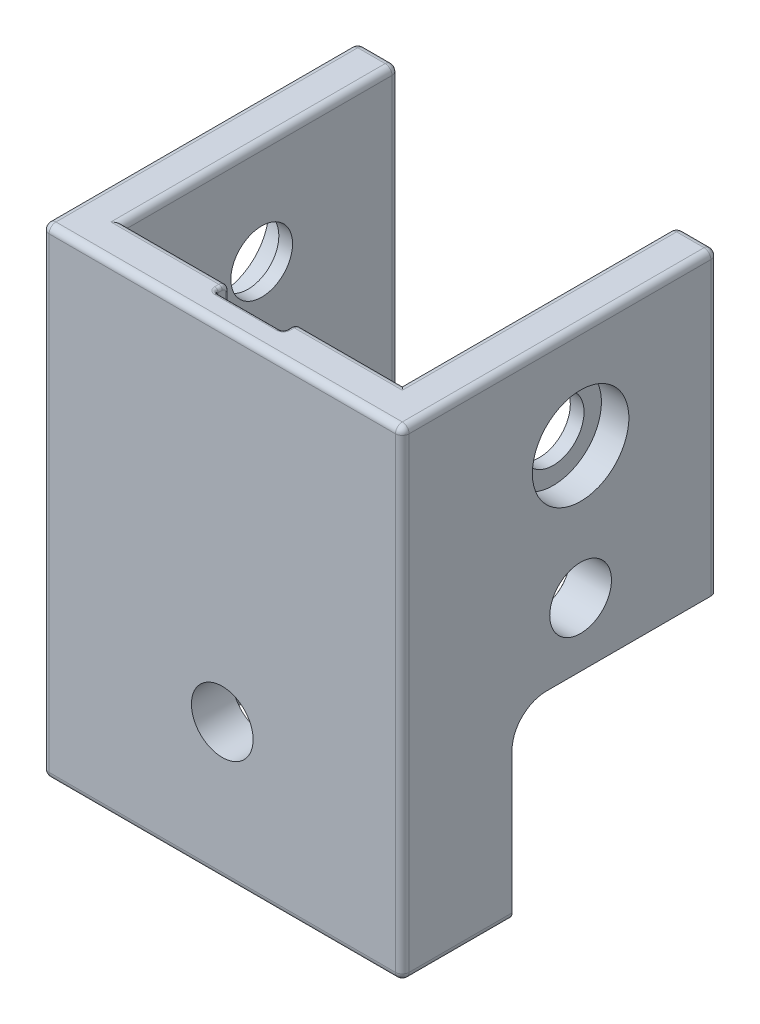
SolidWorks part; units mm, degrees
ref_plane "Front Plane" through (0, 0, 0) normal (0, 0, 1) x (1, 0, 0)
ref_plane "Top Plane" through (0, 0, 0) normal (0, 1, 0) x (1, 0, 0)
ref_plane "Right Plane" through (0, 0, 0) normal (1, 0, 0) x (0, 0, -1)
sketch "Sketch1" plane through (0, 0, 0) normal (0, 1, 0) x (1, 0, 0)
  line L1 (-26.25, -26.25) -> (26.25, -26.25)
  line L2 (-26.25, -26.25) -> (-26.25, 19.75)
  line L4 (26.25, -26.25) -> (26.25, 19.75)
  line L5 (-26.25, -26.25) -> (-20.25, -20.25) construction
  line L6 (20.25, -20.25) -> (26.25, -26.25) construction
  line L11 (-20.25, 19.75) -> (-20.25, -20.25)
  line L12 (-20.25, -20.25) -> (20.25, -20.25)
  line L20 (-20.25, 19.75) -> (-26.25, 19.75)
  line L21 (20.25, 19.75) -> (26.25, 19.75)
  line L22 (20.25, -20.25) -> (20.25, 19.75)
  point P0 (0, 0)
  point P5 (0, 0)
  point P47 (0, 0.8)
  point P49 (0, 0)
  dimension "D1" = 40.5
  dimension "D2" = 6
  dimension "D3" = 6
  dimension "D4" = 46
  dimension "D5" = 6
  dimension "D6" = 46
extrude "Boss-Extrude1" add sketch "Sketch1" along normal blind 70
ref_plane "Plane2" through (20.25, 0, -19.75) normal (1, 0, 0) x (0, 0, -1)
sketch "Sketch8" plane through (26.25, 0, 0) normal (1, 0, 0) x (0, 0, -1)
  line L0 (19.75, 70) -> (19.75, 0) construction
  line L2 (-26.25, 70) -> (19.75, 70) construction
  circle A0 centre (-0.25, 55) radius 4.5
  dimension "D1" = 20
  dimension "D3" = 9
  dimension "D2" = 15
extrude "Cut-Extrude4" cut sketch "Sketch8" against normal through all
sketch "Sketch10" plane through (-26.25, 0, 0) normal (-1, 0, 0) x (0, 0, 1)
  circle A0 centre (0.25, 55) radius 7.035
  dimension "D1" = 14.07
extrude "Cut-Extrude5" cut sketch "Sketch10" against normal blind 4
mirror "Mirror1" about plane through (0, 0, 0) normal (1, 0, 0) of "Cut-Extrude5"
fillet "Fillet13" radius 1 22 edges at (26.25, 0, 3.25) (0, 0, 26.25) (-26.25, 0, 3.25) (-23.25, 0, -19.75) (-26.25, 35, 26.25) (0, 70, 26.25) (-26.25, 70, 3.25) (23.25, 70, -19.75) (-23.25, 70, -19.75) (26.25, 70, 3.25) (26.25, 35, -19.75) (-26.25, 35, -19.75) (26.25, 35, 26.25) (23.25, 0, -19.75) (20.25, 0, 0.25) (-20.25, 0, 0.25) (0, 0, 20.25) (20.25, 70, 0.25) (-20.25, 70, 0.25) (0, 70, 20.25) (-20.25, 35, -19.75) (20.25, 35, -19.75)
sketch "Sketch15" plane through (-26.25, 0, 0) normal (-1, 0, 0) x (0, 0, 1)
  line L0 (-19.75, 1) -> (-19.75, 69) construction
  line L1 (-18.75, 70) -> (25.25, 70) construction
  point P0 (-14.75, 40)
  point P2 (15.25, 40)
  point P4 (15.25, 15)
  point P6 (-14.75, 15)
  dimension "D1" = 5
  dimension "D2" = 35
  dimension "D3" = 25
  dimension "D4" = 30
hole_wizard "M8 Clearance Hole1" positions "Sketch19" profile "Sketch18" hole size "M8" standard "ANSI Metric"
sketch "Sketch19" plane through (-20.25, 0, 0) normal (1, 0, 0) x (0, 0, -1)
  line L0 (19.75, 69) -> (19.75, 1) construction
  point P0 (-0.25, 35.7862)
  point P2 (-0.25, 11.6767)
  point P7 (0, 0)
  dimension "D1" = 20
  dimension "D2" = 20
sketch "Sketch18" plane through (-20.25, 35.7862, 0.25) normal (0, 1, 0) x (0, 0, -1)
  line L0 (0, 0) -> (0, 15.7039)
  line L1 (0, 15.7039) -> (4.5, 13)
  line L2 (4.5, 13) -> (4.5, 0.025)
  line L3 (4.5, 0.025) -> (4.525, 0)
  line L5 (4.525, 0) -> (0, 0)
  line L6 (-4.5, 0.025) -> (-4.525, 0) construction
  line L10 (0, 15.7039) -> (-4.5, 13) construction
  line L11 (0, -6.35) -> (0, 107.95) construction
  dimension "Hole Dia." = 9
  dimension "Hole Depth" = 13
  dimension "Near C'Sink Dia." = 9.05
  dimension "Near C'Sink Angle" = 90
  dimension "Drill Angle" = 118
mirror "Mirror2" about plane through (0, 0, 0) normal (1, 0, 0) of "M8 Clearance Hole1"
ref_plane "Plane3" through (0, 0, 0) normal (1, 0, 0) x (0, 0, -1)
sketch "Sketch20" plane through (0, 0, 0) normal (1, 0, 0) x (0, 0, -1)
  circle A0 centre (-0.25, 55) radius 4.5 construction
  circle A1 centre (-0.25, 55) radius 4.5
sketch "Sketch21" plane through (26.25, 0, 0) normal (-1, 0, 0) x (0, 0, 1)
  line L0 (-19.75, 1) -> (-19.75, -1.1939) construction
  line L1 (-19.75, 0) -> (10.25, 0)
  line L2 (-19.75, 0) -> (-19.75, 26.5)
  line L3 (-19.75, 26.5) -> (10.25, 26.5)
  line L4 (10.25, 0) -> (10.25, 26.5)
  line L5 (-18.5203, 0) -> (-20.9952, 0) construction
  line L6 (25.25, 0) -> (-18.75, 0) construction
  dimension "D1" = 26.5
  dimension "D2" = 30
extrude "Cut-Extrude6" cut sketch "Sketch21" along normal up to next
sketch "Sketch22" plane through (0, 0, 26.25) normal (0, 0, 1) x (1, 0, 0)
  line L0 (0, 0) -> (0, 34.976) construction
  line L1 (0, -21.45) -> (0, 21.45) construction
  line L2 (25.25, 0) -> (-25.25, 0) construction
  point P5 (0, 20)
  dimension "D1" = 20
hole_wizard "M8 Clearance Hole2" positions "Sketch22" profile "Sketch23" hole size "M8" standard "ANSI Metric" end condition through all
sketch "Sketch23" plane through (0, 20, 26.25) normal (1, 0, 0) x (0, -1, 0)
  line L0 (0, 0) -> (0, 46)
  line L1 (0, 46) -> (4.5, 46)
  line L2 (4.5, 46) -> (4.5, 0)
  line L5 (4.5, 0) -> (0, 0)
  line L11 (0, -6.35) -> (0, 107.95) construction
  dimension "Thru Hole Dia." = 9
  dimension "Thru Hole Depth" = 46
fillet "Fillet14" radius 5 1 edges at (23.25, 26.5, 10.25)
sketch "Sketch24" plane through (0, 0, 20.25) normal (0, 0, -1) x (-1, 0, 0)
  line L0 (-21.25, 70) -> (21.25, 70) construction
  line L1 (-5, 32) -> (5, 32)
  line L2 (-5, 32) -> (-5, 70)
  line L3 (-5, 70) -> (5, 70)
  line L4 (5, 32) -> (5, 70)
  line L5 (-5, 32) -> (5, 70) construction
  line L6 (-5, 70) -> (5, 32) construction
  point P0 (0, 51)
  point P7 (0, 32)
  dimension "D1" = 38
  dimension "D2" = 10
extrude "Cut-Extrude7" cut sketch "Sketch24" against normal blind 2.1
fillet "Fillet15" radius 0.5 13 edges at (-5, 69.7071, 20.5429) (5, 69.7071, 20.5429) (5, 70, 21.8) (-5, 70, 21.8) (-5, 50.5, 20.25) (5, 50.5, 20.25) (0, 32, 22.35) (5, 51, 22.35) (0, 70, 22.35) (-5, 51, 22.35) (-5, 32, 21.3) (5, 32, 21.3) (0, 32, 20.25)
